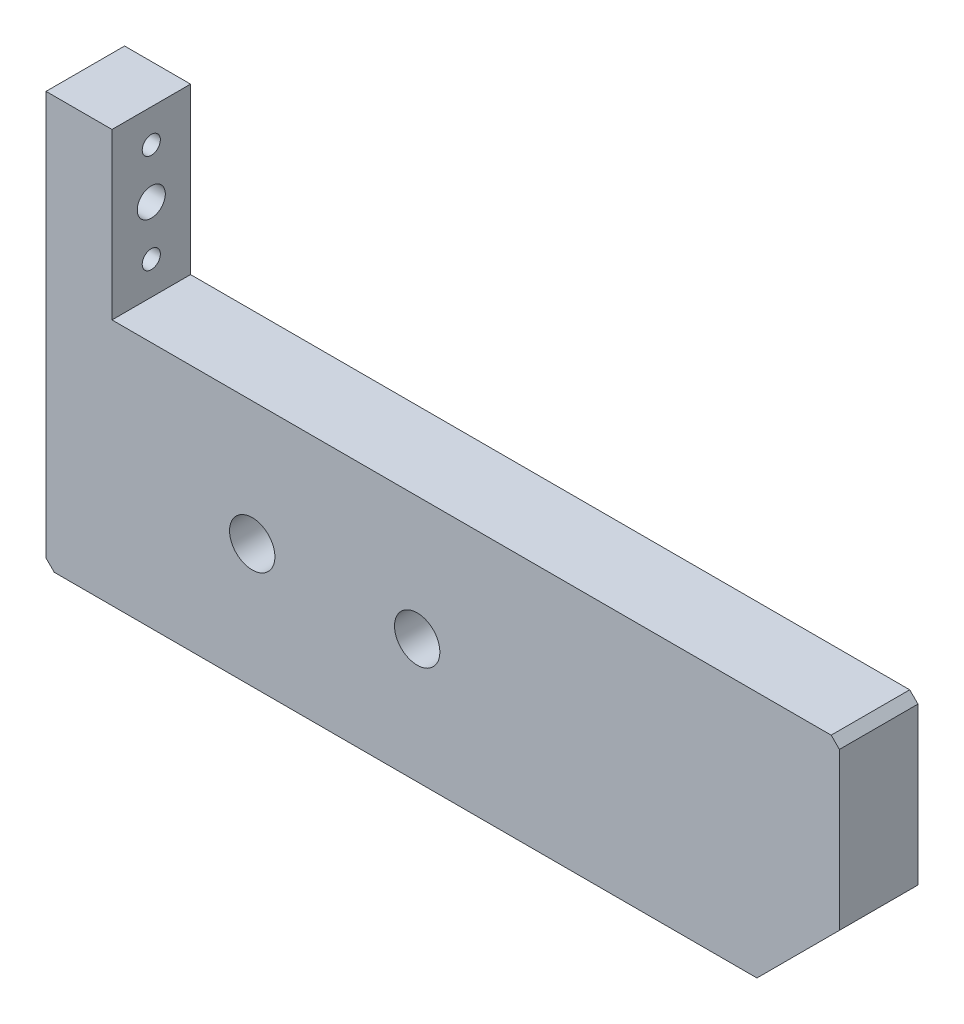
SolidWorks part; units mm, degrees
material "Plain Carbon Steel"
ref_plane "Front Plane" through (0, 0, 0) normal (0, 0, 1) x (1, 0, 0)
ref_plane "Top Plane" through (0, 0, 0) normal (0, 1, 0) x (1, 0, 0)
ref_plane "Right Plane" through (0, 0, 0) normal (1, 0, 0) x (0, 0, -1)
sketch "Sketch1" plane through (0, 0, 0) normal (0, 0, 1) x (1, 0, 0)
  line L5 (-1071, 209.4113) -> (-1071, 239.4113)
  line L6 (-1071, 239.4113) -> (-1159.1924, 239.4113)
  line L7 (-1167.1924, 259.4113) -> (-1167.1924, 209.4113)
  line L8 (-1159.1924, 259.4113) -> (-1167.1924, 259.4113)
  line L9 (-1167.1924, 209.4113) -> (-1071, 209.4113)
  line L10 (-1159.1924, 239.4113) -> (-1159.1924, 259.4113)
  circle A2 centre (-1122.1924, 224.4113) radius 2.75
  circle A3 centre (-1142.1924, 224.4113) radius 2.75
  circle A4 centre (-1142.1924, 224.4113) radius 2.75 construction
  circle A5 centre (-1122.1924, 224.4113) radius 2.75 construction
extrude "Boss-Extrude1" add sketch "Sketch1" along normal up to surface (1 mm away) and the other way up to surface (8.525 mm away)
chamfer "Chamfer1" distance 10 angle 45 1 edges at (-1071, 209.4113, -3.7625)
chamfer "Chamfer2" distance 1 angle 45 2 edges at (-1167.1924, 209.4113, -3.7625) (-1071, 239.4113, -3.7625)
sketch "Sketch2" plane through (-1167.1924, 0, 0) normal (-1, 0, 0) x (0, 0, 1)
  circle A0 centre (-3.7625, 249.4113) radius 1.7
  circle A1 centre (-3.7625, 249.4113) radius 1.5 construction
  dimension "D1" = 3.4
extrude "Cut-Extrude1" cut sketch "Sketch2" against normal through all
sketch "Sketch3" plane through (-1167.1924, 0, 0) normal (-1, 0, 0) x (0, 0, 1)
  line L0 (-3.7625, 243.4113) -> (-3.7625, 255.4113) construction
  line L1 (17.1419, 249.4113) -> (-3.7625, 249.4113) construction
  line L2 (-3.7625, 255.4113) -> (12.0914, 255.4113) construction
  circle A0 centre (-3.7625, 255.4113) radius 1.1
  circle A1 centre (-3.7625, 243.4113) radius 1.1
  circle A3 centre (-3.7625, 249.4113) radius 1.7 construction
  dimension "D1" = 2.2
  dimension "D2" = 6
extrude "Cut-Extrude2" cut sketch "Sketch3" against normal through all
sketch "Sketch4" plane through (-1167.1924, 0, 0) normal (-1, 0, 0) x (0, 0, 1)
  circle A0 centre (-3.7625, 249.4113) radius 3.175
  dimension "D1" = 6.35
extrude "Cut-Extrude3" cut sketch "Sketch4" against normal blind 3
